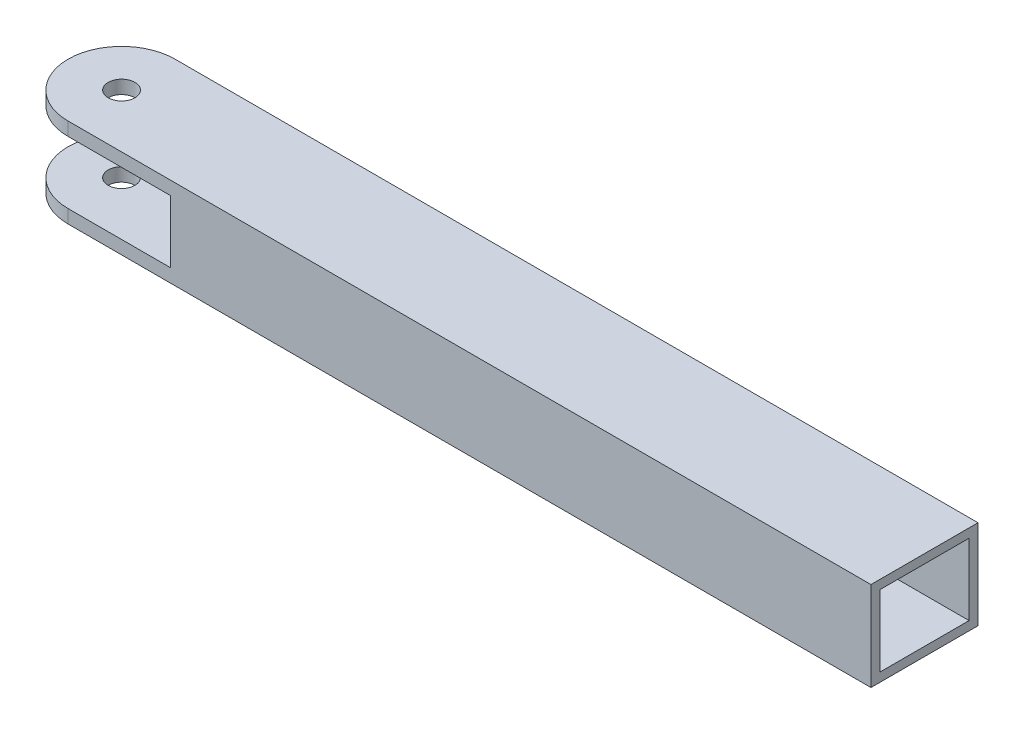
SolidWorks part; units mm, degrees
ref_plane "Płaszczyzna przednia" through (0, 0, 0) normal (0, 0, 1) x (1, 0, 0)
ref_plane "Płaszczyzna górna" through (0, 0, 0) normal (0, 1, 0) x (1, 0, 0)
ref_plane "Płaszczyzna prawa" through (0, 0, 0) normal (1, 0, 0) x (0, 0, -1)
sketch "Szkic1" plane through (0, 0, 0) normal (0, 1, 0) x (1, 0, 0)
  line L1 (0, 6) -> (90, 6)
  line L2 (0, -6) -> (90, -6)
  line L4 (90, 6) -> (90, -6)
  circle A0 centre (0, 0) radius 1.5
  arc A1 (0, 6) -> (0, -6) centre (0, 0) ccw
  point P3 (37.5, 0)
  dimension "D1" = 3
  dimension "D2" = 6
  dimension "D3" = 90
extrude "Dodanie-wyciągnięcie1" add sketch "Szkic1" along normal blind 10
sketch "Szkic2" plane through (0, 0, -6) normal (0, 0, -1) x (-1, 0, 0)
  line L8 (-11.5, 8.5) -> (23.5, 8.5)
  line L9 (-11.5, 8.5) -> (-11.5, 1.5)
  line L10 (-11.5, 1.5) -> (23.5, 1.5)
  line L11 (23.5, 8.5) -> (23.5, 1.5)
  line L12 (-11.5, 8.5) -> (23.5, 1.5) construction
  line L13 (-11.5, 1.5) -> (23.5, 8.5) construction
  line L14 (6, 0) -> (6, 10) construction
  point P7 (6, 5)
  dimension "D1" = 8.5
  dimension "D2" = 7
  dimension "D3" = 35
extrude "Wytnij-wyciągnięcie1" cut sketch "Szkic2" against normal through all
sketch "Szkic3" plane through (90, 0, 0) normal (1, 0, 0) x (0, 0, -1)
  line L17 (-5, 1) -> (5, 1)
  line L18 (5, 1) -> (5, 9)
  line L19 (5, 9) -> (-5, 9)
  line L20 (-5, 9) -> (-5, 1)
  line L21 (-5, 1) -> (5, 1)
  line L22 (5, 1) -> (5, 9)
  line L23 (5, 9) -> (-5, 9)
  line L24 (-5, 9) -> (-5, 1)
  dimension "D1" = 1
extrude "Wytnij-wyciągnięcie2" cut sketch "Szkic3" against normal blind 75 contours L23 L24 L21 L22
